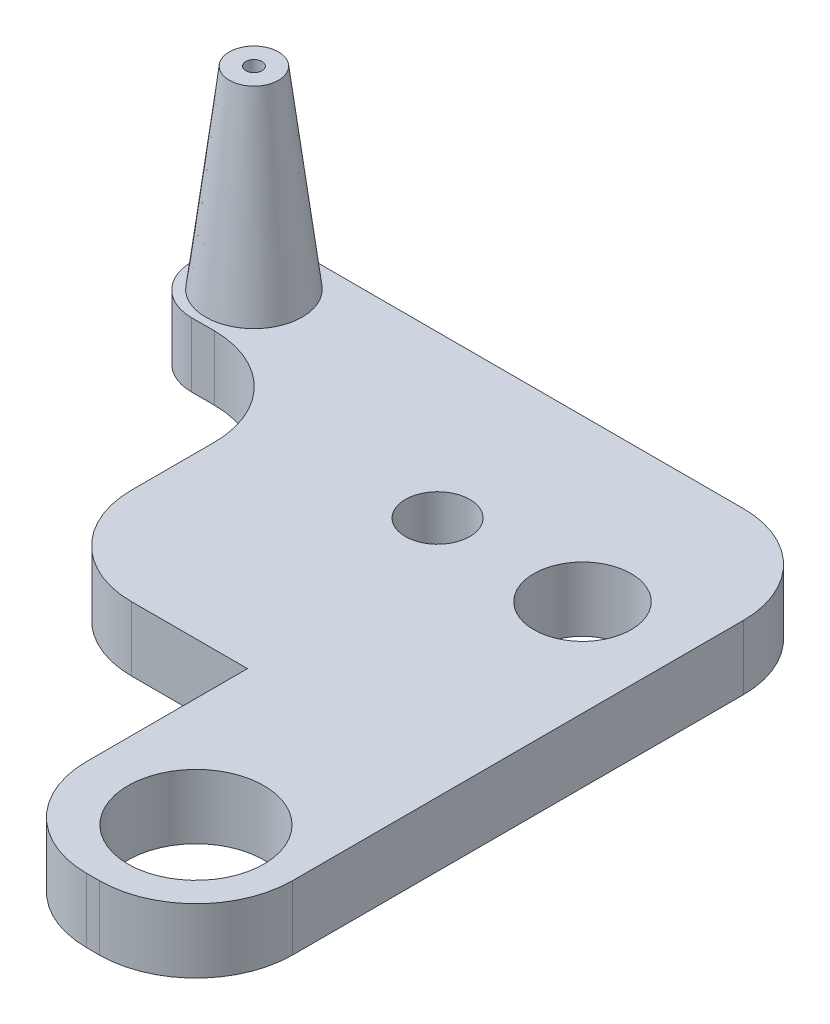
SolidWorks part; units mm, degrees
ref_plane "Front Plane" through (0, 0, 0) normal (0, 0, 1) x (1, 0, 0)
ref_plane "Top Plane" through (0, 0, 0) normal (0, 1, 0) x (1, 0, 0)
ref_plane "Right Plane" through (0, 0, 0) normal (1, 0, 0) x (0, 0, -1)
sketch "Sketch1" plane through (0, 0, 0) normal (0, 1, 0) x (1, 0, 0)
  line L0 (23.9959, -35) -> (56.9959, -35)
  line L4 (88.9959, -25) -> (88.9959, 25)
  line L5 (0, -39.6238) -> (0, 46.4731) construction
  line L6 (23.9959, 0) -> (23.9959, -35)
  line L7 (56.9959, -75) -> (88.9959, -75)
  line L8 (88.9959, -75) -> (88.9959, -25)
  line L10 (17.5, 25) -> (88.9959, 25)
  line L11 (73.9959, 41.1849) -> (73.9959, -116.2589) construction
  line L16 (17.5, 25) -> (-2.0041, 25)
  line L17 (-2.0041, 25) -> (-2.0041, 7.8405)
  line L19 (23.9959, 0) -> (23.9959, 7.8405)
  line L20 (23.9959, 7.8405) -> (-2.0041, 7.8405)
  line L21 (23.9959, 0) -> (73.9959, 0) construction
  line L22 (56.9959, -35) -> (56.9959, -75)
  circle A6 centre (73.9959, 0) radius 7.55
  circle A7 centre (51.4959, 0) radius 5
  circle A9 centre (73.9959, -60) radius 10.55
  circle A10 centre (5.147, 17.7557) radius 2.5 construction
  point P0 (0, 0)
  point P12 (0, 0)
  point P16 (23.9959, -36.894)
  dimension "D3" = 22.5
  dimension "D5" = 100
  dimension "D7" = 15.1
  dimension "D4" = 10
  dimension "D1" = 60
  dimension "D8" = 21.1
  dimension "D13" = 5
  dimension "D6" = 91
  dimension "D9" = 15
  dimension "D10" = 50
  dimension "D11" = 32
extrude "Boss-Extrude1" add sketch "Sketch1" along normal blind 10
sketch "Sketch4" plane through (0, 10, 0) normal (0, 1, 0) x (1, 0, 0)
  line L2 (88.9959, 25) -> (-2.0041, 25) construction
  line L3 (-2.0041, 25) -> (-2.0041, 7.8405) construction
  circle A0 centre (6.4959, 16.5) radius 7.5
  dimension "D1" = 15
  dimension "D2" = 8.5
  dimension "D3" = 8.5
extrude "Boss-Extrude2" add sketch "Sketch4" along normal blind 30 draft 7 contours A0
sketch "Sketch5" plane through (0, 40, 0) normal (0, 1, 0) x (1, 0, 0)
  line L0 (-2.0041, 25) -> (-2.0041, 7.8405) construction
  line L1 (88.9959, 25) -> (-2.0041, 25) construction
  circle A0 centre (6.4959, 16.5) radius 1.25
  dimension "D1" = 8.5
  dimension "D2" = 8.5
  dimension "D3" = 2.5
extrude "Cut-Extrude2" cut sketch "Sketch5" against normal blind 10
fillet "Fillet1" radius 15 5 edges at (23.9959, 5, -7.8405) (88.9959, 5, -25) (88.9959, 5, 75) (56.9959, 5, 75) (23.9959, 5, 35)
fillet "Fillet2" radius 7.5 2 edges at (-2.0041, 5, -7.8405) (-2.0041, 5, -25)
